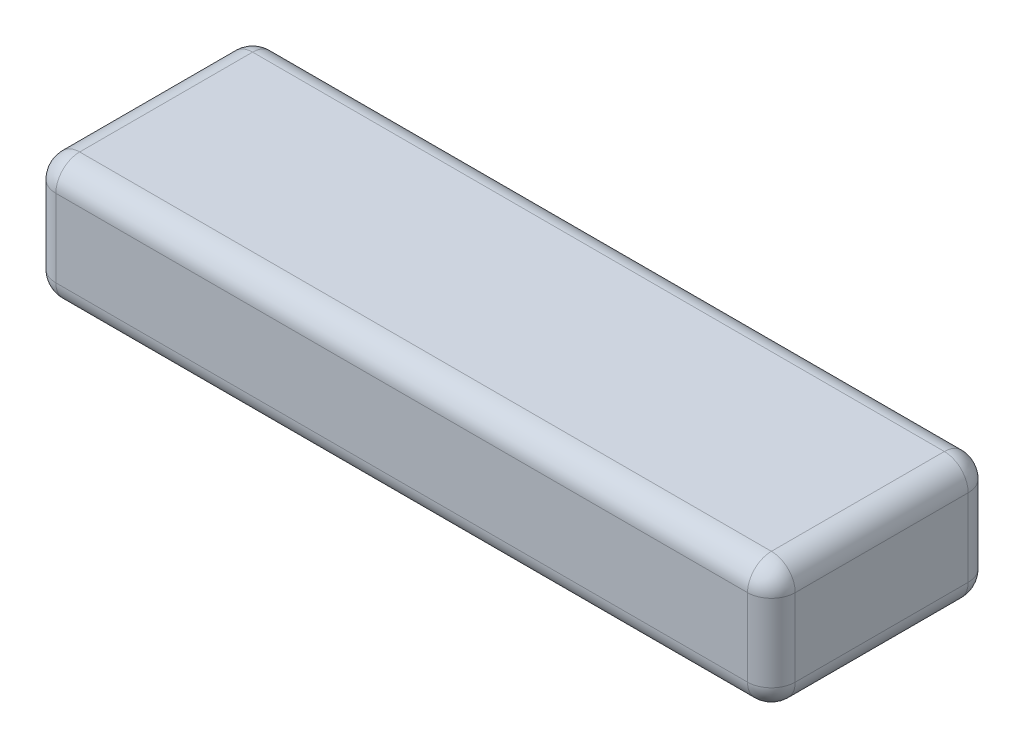
SolidWorks part; units mm, degrees
ref_plane "Front Plane" through (0, 0, 0) normal (0, 0, 1) x (1, 0, 0)
ref_plane "Top Plane" through (0, 0, 0) normal (0, 1, 0) x (1, 0, 0)
ref_plane "Right Plane" through (0, 0, 0) normal (1, 0, 0) x (0, 0, -1)
sketch "Sketch1" plane through (0, 0, 0) normal (0, 1, 0) x (1, 0, 0)
  line L1 (-31, 9.25) -> (31, 9.25)
  line L2 (-31, 9.25) -> (-31, -9.25)
  line L3 (-31, -9.25) -> (31, -9.25)
  line L4 (31, 9.25) -> (31, -9.25)
  line L5 (-31, 9.25) -> (31, -9.25) construction
  line L6 (-31, -9.25) -> (31, 9.25) construction
  point P0 (0, 0)
  dimension "D1" = 62
  dimension "D2" = 18.5
extrude "Boss-Extrude1" add sketch "Sketch1" along normal mid plane 10.5
fillet "Fillet1" radius 2 12 edges at (0, -5.25, -9.25) (-31, -5.25, 0) (0, -5.25, 9.25) (31, -5.25, 0) (0, 5.25, 9.25) (-31, 5.25, 0) (0, 5.25, -9.25) (31, 5.25, 0) (31, 0, -9.25) (31, 0, 9.25) (-31, 0, -9.25) (-31, 0, 9.25)
